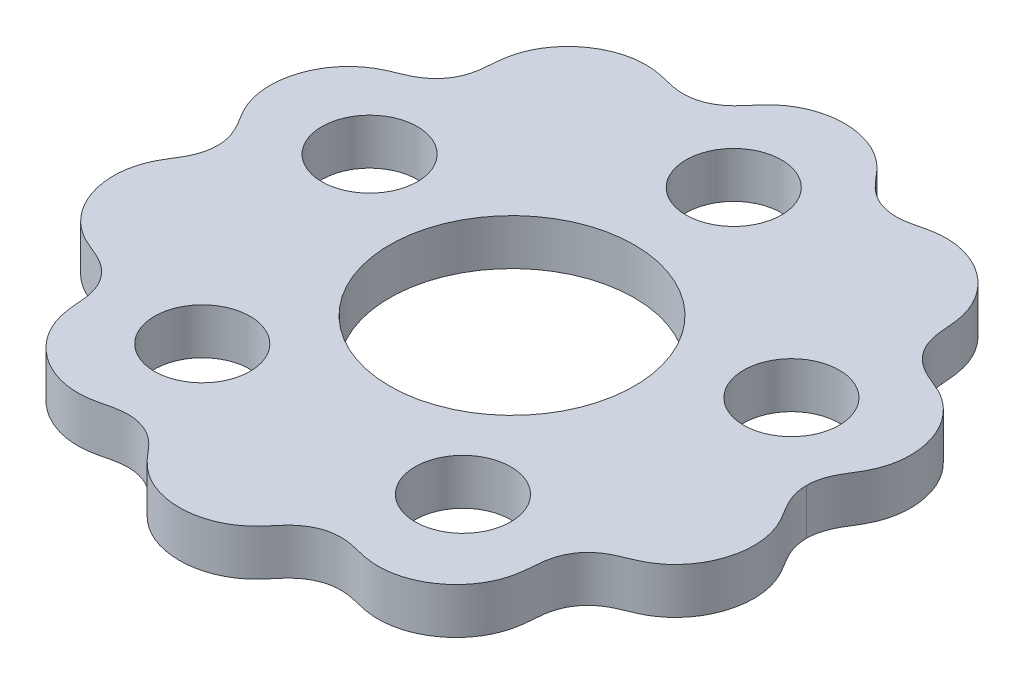
SolidWorks part; units mm, degrees
material "PET"
ref_plane "Front Plane" through (0, 0, 0) normal (0, 0, 1) x (1, 0, 0)
ref_plane "Top Plane" through (0, 0, 0) normal (0, 1, 0) x (1, 0, 0)
ref_plane "Right Plane" through (0, 0, 0) normal (1, 0, 0) x (0, 0, -1)
sketch "Sketch1" plane through (0, 0, 0) normal (0, 1, 0) x (1, 0, 0)
  line L0 (-38.5, 0) -> (38.5, 0) construction
  spline S0 degree 4 poles (41.7399, 11.9357) (41.7976, 11.5909) (41.8823, 10.8959) (41.9166, 9.7895) (41.7622, 8.4507) (41.4548, 7.254) (41.0605, 6.2518) (40.6722, 5.4784) (40.2556, 4.7734) (39.8948, 4.2014) (39.5954, 3.7049) (39.3601, 3.2778) (39.1827, 2.9244) (39.0201, 2.559) (38.8752, 2.1815) (38.7672, 1.8445) (38.689, 1.5515) (38.6338, 1.305) (38.5956, 1.1064) (38.5637, 0.9069) (38.5413, 0.7307) (38.526, 0.5807) (38.516, 0.4563) (38.5095, 0.3545) (38.5047, 0.2479) (38.5015, 0.1386) (38.4995, 0.0148) (38.5001, -0.0789) (38.5036, -0.2237) (38.5098, -0.3594) (38.5164, -0.4628) (38.5267, -0.5886) (38.5424, -0.7399) (38.5653, -0.918) (38.5978, -1.1189) (38.6366, -1.3186) (38.6815, -1.5171) (38.7324, -1.714) (38.8035, -1.9582) (38.914, -2.2894) (39.0778, -2.7023) (39.3093, -3.1893) (39.5914, -3.6994) (39.9929, -4.3618) (40.5108, -5.1772) (41.094, -6.2603) (41.6193, -7.7231) (41.9033, -9.3234) (41.9104, -11.0174) (41.6357, -12.7107) (41.1099, -14.3049) (40.2814, -15.8994) (39.2956, -17.1747) (38.2761, -18.1324) (37.3157, -18.8177) (36.5643, -19.2568) (35.7841, -19.6295) (34.9889, -19.9536) (34.1836, -20.2802) (33.3903, -20.6628) (32.4577, -21.2405) (31.5077, -22.0772) (30.6676, -23.2287) (30.0983, -24.6485) (29.8484, -26.052) (29.7811, -27.3474) (29.672, -28.5202) (29.4293, -29.7204) (28.992, -31.0294) (28.1243, -32.7018) (26.8403, -34.2468) (25.2758, -35.4915) (23.478, -36.4327) (21.9132, -36.9493) (20.3645, -37.183) (18.8855, -37.1588) (17.6433, -36.9754) (16.4953, -36.6867) (15.2652, -36.3845) (13.9169, -36.2413) (12.4319, -36.3844) (11.0762, -36.8709) (9.9712, -37.5729) (9.1322, -38.3356) (8.5282, -39.0054) (7.9812, -39.6642) (7.4483, -40.2769) (6.716, -41.018) (5.6675, -41.866) (4.292, -42.6513) (2.5792, -43.2464) (0.7931, -43.5294) (-0.9374, -43.5172) (-2.6957, -43.2137) (-4.3731, -42.6106) (-5.7196, -41.8284) (-6.7475, -40.9896) (-7.477, -40.2457) (-8.0111, -39.6284) (-8.5572, -38.9713) (-9.1586, -38.3097) (-9.9918, -37.5589) (-11.087, -36.8668) (-12.4351, -36.3841) (-13.9169, -36.2413) (-15.2652, -36.3845) (-16.4953, -36.6867) (-17.6432, -36.9755) (-18.8855, -37.1588) (-20.1014, -37.1787) (-21.2828, -37.0443) (-22.5182, -36.7497) (-23.7112, -36.3106) (-25.2757, -35.4916) (-26.8404, -34.2467) (-28.1243, -32.7018) (-28.992, -31.0294) (-29.4293, -29.7204) (-29.672, -28.5202) (-29.7811, -27.3474) (-29.8484, -26.052) (-30.0983, -24.6485) (-30.6676, -23.2287) (-31.5077, -22.0772) (-32.4577, -21.2405) (-33.3903, -20.6628) (-34.1836, -20.2802) (-34.9889, -19.9536) (-35.7841, -19.6295) (-36.5643, -19.2568) (-37.3157, -18.8177) (-38.2761, -18.1324) (-39.2956, -17.1747) (-40.2814, -15.8994) (-41.2689, -13.9989) (-41.8434, -11.9655) (-41.9616, -10.0978) (-41.7583, -8.4939) (-41.4838, -7.3945) (-41.1825, -6.5281) (-40.8054, -5.7182) (-40.373, -4.9656) (-39.9705, -4.3209) (-39.6284, -3.7649) (-39.3439, -3.2554) (-39.12, -2.7926) (-38.9499, -2.3821) (-38.824, -2.0287) (-38.7172, -1.6695) (-38.6304, -1.304) (-38.5728, -0.9818) (-38.5369, -0.7009) (-38.5162, -0.4703) (-38.5051, -0.2842) (-38.4994, -0.0606) (-38.4996, 0.072) (-38.5059, 0.3106) (-38.5188, 0.5048) (-38.5357, 0.6806) (-38.5541, 0.8315) (-38.5757, 0.9817) (-38.6004, 1.1312) (-38.6338, 1.3049) (-38.689, 1.5516) (-38.7672, 1.8445) (-38.8752, 2.1815) (-39.0201, 2.559) (-39.1827, 2.9244) (-39.3601, 3.2778) (-39.5954, 3.7049) (-39.8948, 4.2014) (-40.2556, 4.7734) (-40.6722, 5.4784) (-41.0605, 6.2518) (-41.4548, 7.254) (-41.7622, 8.4507) (-41.9166, 9.7895) (-41.8823, 10.8959) (-41.7976, 11.5909) (-41.7399, 11.9357) knots 0 0 0 0 0 0.008359 0.016718 0.026378 0.03209 0.037801 0.04242 0.047039 0.051658 0.053968 0.056277 0.058692 0.061108 0.063523 0.065938 0.067146 0.068354 0.069562 0.07077 0.071978 0.072582 0.073186 0.07379 0.074394 0.074998 0.075602 0.076827 0.077439 0.078051 0.078663 0.079275 0.080499 0.081715 0.08293 0.084146 0.085361 0.086577 0.087792 0.090223 0.093706 0.097188 0.10067 0.104152 0.112217 0.120283 0.129997 0.141148 0.150862 0.160575 0.170839 0.181103 0.193621 0.198878 0.204135 0.209266 0.214397 0.219527 0.224658 0.230039 0.23542 0.245691 0.254714 0.26373 0.271663 0.279595 0.285726 0.291856 0.300873 0.312488 0.330522 0.339406 0.34829 0.360829 0.369712 0.376626 0.383539 0.39077 0.398002 0.40689 0.415781 0.426124 0.432044 0.437965 0.442816 0.447666 0.452516 0.457367 0.4677 0.4798 0.490134 0.500468 0.510727 0.520985 0.53259 0.542848 0.547724 0.5526 0.557476 0.562352 0.568152 0.573952 0.584219 0.59311 0.601998 0.60923 0.616461 0.623374 0.630288 0.639171 0.645441 0.65171 0.660594 0.669478 0.687512 0.699127 0.708144 0.714274 0.720405 0.728337 0.73627 0.745286 0.754309 0.76458 0.769961 0.775342 0.780473 0.785603 0.790734 0.795865 0.801122 0.806379 0.818897 0.829161 0.839425 0.857344 0.868978 0.873457 0.877937 0.884404 0.89087 0.894771 0.898672 0.902573 0.906473 0.908713 0.910953 0.913192 0.915432 0.917673 0.919915 0.921035 0.922156 0.923277 0.924398 0.925606 0.926814 0.928022 0.92923 0.929834 0.930438 0.931646 0.932854 0.934062 0.936477 0.938892 0.941308 0.943723 0.946032 0.948342 0.952961 0.95758 0.962199 0.96791 0.973622 0.983282 0.991641 1 1 1 1 1 construction
  spline S1 degree 4 poles (38.5, 0) (38.5, -0.0435) (38.5008, -0.1075) (38.5036, -0.2237) (38.5098, -0.3594) (38.5164, -0.4628) (38.5267, -0.5886) (38.5424, -0.7399) (38.5653, -0.918) (38.5978, -1.1189) (38.6366, -1.3186) (38.6815, -1.5171) (38.7324, -1.714) (38.8035, -1.9582) (38.914, -2.2894) (39.0778, -2.7023) (39.3093, -3.1893) (39.5914, -3.6994) (39.9929, -4.3618) (40.5108, -5.1772) (41.094, -6.2603) (41.6193, -7.7231) (41.9033, -9.3234) (41.9104, -11.0174) (41.6357, -12.7107) (41.1099, -14.3049) (40.2814, -15.8994) (39.2956, -17.1747) (38.2761, -18.1324) (37.3157, -18.8177) (36.5643, -19.2568) (35.7841, -19.6295) (34.9889, -19.9536) (34.1836, -20.2802) (33.3903, -20.6628) (32.4577, -21.2405) (31.5077, -22.0772) (30.6676, -23.2287) (30.0983, -24.6485) (29.8484, -26.052) (29.7811, -27.3474) (29.672, -28.5202) (29.4293, -29.7204) (28.992, -31.0294) (28.1243, -32.7018) (26.8403, -34.2468) (25.2758, -35.4915) (23.478, -36.4327) (21.9132, -36.9493) (20.3645, -37.183) (18.8855, -37.1588) (17.6433, -36.9754) (16.4953, -36.6867) (15.2652, -36.3845) (13.9169, -36.2413) (12.4319, -36.3844) (11.0762, -36.8709) (9.9712, -37.5729) (9.1322, -38.3356) (8.5282, -39.0054) (7.9812, -39.6642) (7.4483, -40.2769) (6.716, -41.018) (5.6675, -41.866) (4.292, -42.6513) (2.5792, -43.2464) (0.7931, -43.5294) (-0.9374, -43.5172) (-2.6957, -43.2137) (-4.3731, -42.6106) (-5.7196, -41.8284) (-6.7475, -40.9896) (-7.477, -40.2457) (-8.0111, -39.6284) (-8.5572, -38.9713) (-9.1586, -38.3097) (-9.9918, -37.5589) (-11.087, -36.8668) (-12.4351, -36.3841) (-13.9169, -36.2413) (-15.2652, -36.3845) (-16.4953, -36.6867) (-17.6432, -36.9755) (-18.8855, -37.1588) (-20.1014, -37.1787) (-21.2828, -37.0443) (-22.5182, -36.7497) (-23.7112, -36.3106) (-25.2757, -35.4916) (-26.8404, -34.2467) (-28.1243, -32.7018) (-28.992, -31.0294) (-29.4293, -29.7204) (-29.672, -28.5202) (-29.7811, -27.3474) (-29.8484, -26.052) (-30.0983, -24.6485) (-30.6676, -23.2287) (-31.5077, -22.0772) (-32.4577, -21.2405) (-33.3903, -20.6628) (-34.1836, -20.2802) (-34.9889, -19.9536) (-35.7841, -19.6295) (-36.5643, -19.2568) (-37.3157, -18.8177) (-38.2761, -18.1324) (-39.2956, -17.1747) (-40.2814, -15.8994) (-41.2689, -13.9989) (-41.8434, -11.9655) (-41.9616, -10.0978) (-41.7583, -8.4939) (-41.4838, -7.3945) (-41.1825, -6.5281) (-40.8054, -5.7182) (-40.373, -4.9656) (-39.9705, -4.3209) (-39.6284, -3.7649) (-39.3439, -3.2554) (-39.12, -2.7926) (-38.9499, -2.3821) (-38.824, -2.0287) (-38.7172, -1.6695) (-38.6304, -1.304) (-38.5728, -0.9818) (-38.5369, -0.7009) (-38.5162, -0.4703) (-38.5051, -0.2842) (-38.5009, -0.1197) (-38.5, -0.0398) (-38.5, 0) knots 0.075602 0.075602 0.075602 0.075602 0.075602 0.076827 0.077439 0.078051 0.078663 0.079275 0.080499 0.081715 0.08293 0.084146 0.085361 0.086577 0.087792 0.090223 0.093706 0.097188 0.10067 0.104152 0.112217 0.120283 0.129997 0.141148 0.150862 0.160575 0.170839 0.181103 0.193621 0.198878 0.204135 0.209266 0.214397 0.219527 0.224658 0.230039 0.23542 0.245691 0.254714 0.26373 0.271663 0.279595 0.285726 0.291856 0.300873 0.312488 0.330522 0.339406 0.34829 0.360829 0.369712 0.376626 0.383539 0.39077 0.398002 0.40689 0.415781 0.426124 0.432044 0.437965 0.442816 0.447666 0.452516 0.457367 0.4677 0.4798 0.490134 0.500468 0.510727 0.520985 0.53259 0.542848 0.547724 0.5526 0.557476 0.562352 0.568152 0.573952 0.584219 0.59311 0.601998 0.60923 0.616461 0.623374 0.630288 0.639171 0.645441 0.65171 0.660594 0.669478 0.687512 0.699127 0.708144 0.714274 0.720405 0.728337 0.73627 0.745286 0.754309 0.76458 0.769961 0.775342 0.780473 0.785603 0.790734 0.795865 0.801122 0.806379 0.818897 0.829161 0.839425 0.857344 0.868978 0.873457 0.877937 0.884404 0.89087 0.894771 0.898672 0.902573 0.906473 0.908713 0.910953 0.913192 0.915432 0.917673 0.919915 0.921035 0.922156 0.923277 0.924398 0.924398 0.924398 0.924398 0.924398
  spline S3 degree 4 poles (38.5, 0) (38.5, 0.0435) (38.5008, 0.1075) (38.5036, 0.2237) (38.5098, 0.3594) (38.5164, 0.4628) (38.5267, 0.5886) (38.5424, 0.7399) (38.5653, 0.918) (38.5978, 1.1189) (38.6366, 1.3186) (38.6815, 1.5171) (38.7324, 1.714) (38.8035, 1.9582) (38.914, 2.2894) (39.0778, 2.7023) (39.3093, 3.1893) (39.5914, 3.6994) (39.9929, 4.3618) (40.5108, 5.1772) (41.094, 6.2603) (41.6193, 7.7231) (41.9033, 9.3234) (41.9104, 11.0174) (41.6357, 12.7107) (41.1099, 14.3049) (40.2814, 15.8994) (39.2956, 17.1747) (38.2761, 18.1324) (37.3157, 18.8177) (36.5643, 19.2568) (35.7841, 19.6295) (34.9889, 19.9536) (34.1836, 20.2802) (33.3903, 20.6628) (32.4577, 21.2405) (31.5077, 22.0772) (30.6676, 23.2287) (30.0983, 24.6485) (29.8484, 26.052) (29.7811, 27.3474) (29.672, 28.5202) (29.4293, 29.7204) (28.992, 31.0294) (28.1243, 32.7018) (26.8403, 34.2468) (25.2758, 35.4915) (23.478, 36.4327) (21.9132, 36.9493) (20.3645, 37.183) (18.8855, 37.1588) (17.6433, 36.9754) (16.4953, 36.6867) (15.2652, 36.3845) (13.9169, 36.2413) (12.4319, 36.3844) (11.0762, 36.8709) (9.9712, 37.5729) (9.1322, 38.3356) (8.5282, 39.0054) (7.9812, 39.6642) (7.4483, 40.2769) (6.716, 41.018) (5.6675, 41.866) (4.292, 42.6513) (2.5792, 43.2464) (0.7931, 43.5294) (-0.9374, 43.5172) (-2.6957, 43.2137) (-4.3731, 42.6106) (-5.7196, 41.8284) (-6.7475, 40.9896) (-7.477, 40.2457) (-8.0111, 39.6284) (-8.5572, 38.9713) (-9.1586, 38.3097) (-9.9918, 37.5589) (-11.087, 36.8668) (-12.4351, 36.3841) (-13.9169, 36.2413) (-15.2652, 36.3845) (-16.4953, 36.6867) (-17.6432, 36.9755) (-18.8855, 37.1588) (-20.1014, 37.1787) (-21.2828, 37.0443) (-22.5182, 36.7497) (-23.7112, 36.3106) (-25.2757, 35.4916) (-26.8404, 34.2467) (-28.1243, 32.7018) (-28.992, 31.0294) (-29.4293, 29.7204) (-29.672, 28.5202) (-29.7811, 27.3474) (-29.8484, 26.052) (-30.0983, 24.6485) (-30.6676, 23.2287) (-31.5077, 22.0772) (-32.4577, 21.2405) (-33.3903, 20.6628) (-34.1836, 20.2802) (-34.9889, 19.9536) (-35.7841, 19.6295) (-36.5643, 19.2568) (-37.3157, 18.8177) (-38.2761, 18.1324) (-39.2956, 17.1747) (-40.2814, 15.8994) (-41.2689, 13.9989) (-41.8434, 11.9655) (-41.9616, 10.0978) (-41.7583, 8.4939) (-41.4838, 7.3945) (-41.1825, 6.5281) (-40.8054, 5.7182) (-40.373, 4.9656) (-39.9705, 4.3209) (-39.6284, 3.7649) (-39.3439, 3.2554) (-39.12, 2.7926) (-38.9499, 2.3821) (-38.824, 2.0287) (-38.7172, 1.6695) (-38.6304, 1.304) (-38.5728, 0.9818) (-38.5369, 0.7009) (-38.5162, 0.4703) (-38.5051, 0.2842) (-38.5009, 0.1197) (-38.5, 0.0398) (-38.5, 0) knots 0.075602 0.075602 0.075602 0.075602 0.075602 0.076827 0.077439 0.078051 0.078663 0.079275 0.080499 0.081715 0.08293 0.084146 0.085361 0.086577 0.087792 0.090223 0.093706 0.097188 0.10067 0.104152 0.112217 0.120283 0.129997 0.141148 0.150862 0.160575 0.170839 0.181103 0.193621 0.198878 0.204135 0.209266 0.214397 0.219527 0.224658 0.230039 0.23542 0.245691 0.254714 0.26373 0.271663 0.279595 0.285726 0.291856 0.300873 0.312488 0.330522 0.339406 0.34829 0.360829 0.369712 0.376626 0.383539 0.39077 0.398002 0.40689 0.415781 0.426124 0.432044 0.437965 0.442816 0.447666 0.452516 0.457367 0.4677 0.4798 0.490134 0.500468 0.510727 0.520985 0.53259 0.542848 0.547724 0.5526 0.557476 0.562352 0.568152 0.573952 0.584219 0.59311 0.601998 0.60923 0.616461 0.623374 0.630288 0.639171 0.645441 0.65171 0.660594 0.669478 0.687512 0.699127 0.708144 0.714274 0.720405 0.728337 0.73627 0.745286 0.754309 0.76458 0.769961 0.775342 0.780473 0.785603 0.790734 0.795865 0.801122 0.806379 0.818897 0.829161 0.839425 0.857344 0.868978 0.873457 0.877937 0.884404 0.89087 0.894771 0.898672 0.902573 0.906473 0.908713 0.910953 0.913192 0.915432 0.917673 0.919915 0.921035 0.922156 0.923277 0.924398 0.924398 0.924398 0.924398 0.924398
extrude "Boss-Extrude1" add sketch "Sketch1" along normal blind 6
sketch "Sketch2" plane through (0, 6, 0) normal (0, 1, 0) x (1, 0, 0)
  line L0 (0, 0) -> (38.5, 0) construction
  line L1 (0, 0) -> (41.371, 13.4423) construction
  circle A0 centre (0, 0) radius 16
  circle A1 centre (27.5801, 8.9631) radius 6.25
  circle A2 centre (17.0471, -23.4605) radius 6.25
  circle A3 centre (-17.0444, -23.4625) radius 6.25
  circle A4 centre (-27.5812, 8.9599) radius 6.25
  circle A5 centre (-0.0017, 29) radius 6.25
  spline S1 degree 4 poles (38.5, 0) (38.5, 0.0435) (38.5008, 0.1075) (38.5036, 0.2237) (38.5098, 0.3594) (38.5164, 0.4628) (38.5267, 0.5886) (38.5424, 0.7399) (38.5653, 0.918) (38.5978, 1.1189) (38.6366, 1.3186) (38.6815, 1.5171) (38.7324, 1.714) (38.8035, 1.9582) (38.914, 2.2894) (39.0778, 2.7023) (39.3093, 3.1893) (39.5914, 3.6994) (39.9929, 4.3618) (40.5108, 5.1772) (41.094, 6.2603) (41.6193, 7.7231) (41.9033, 9.3234) (41.9104, 11.0174) (41.6357, 12.7107) (41.1099, 14.3049) (40.2814, 15.8994) (39.2956, 17.1747) (38.2761, 18.1324) (37.3157, 18.8177) (36.5643, 19.2568) (35.7841, 19.6295) (34.9889, 19.9536) (34.1836, 20.2802) (33.3903, 20.6628) (32.4577, 21.2405) (31.5077, 22.0772) (30.6676, 23.2287) (30.0983, 24.6485) (29.8484, 26.052) (29.7811, 27.3474) (29.672, 28.5202) (29.4293, 29.7204) (28.992, 31.0294) (28.1243, 32.7018) (26.8403, 34.2468) (25.2758, 35.4915) (23.478, 36.4327) (21.9132, 36.9493) (20.3645, 37.183) (18.8855, 37.1588) (17.6433, 36.9754) (16.4953, 36.6867) (15.2652, 36.3845) (13.9169, 36.2413) (12.4319, 36.3844) (11.0762, 36.8709) (9.9712, 37.5729) (9.1322, 38.3356) (8.5282, 39.0054) (7.9812, 39.6642) (7.4483, 40.2769) (6.716, 41.018) (5.6675, 41.866) (4.292, 42.6513) (2.5792, 43.2464) (0.7931, 43.5294) (-0.9374, 43.5172) (-2.6957, 43.2137) (-4.3731, 42.6106) (-5.7196, 41.8284) (-6.7475, 40.9896) (-7.477, 40.2457) (-8.0111, 39.6284) (-8.5572, 38.9713) (-9.1586, 38.3097) (-9.9918, 37.5589) (-11.087, 36.8668) (-12.4351, 36.3841) (-13.9169, 36.2413) (-15.2652, 36.3845) (-16.4953, 36.6867) (-17.6432, 36.9755) (-18.8855, 37.1588) (-20.1014, 37.1787) (-21.2828, 37.0443) (-22.5182, 36.7497) (-23.7112, 36.3106) (-25.2757, 35.4916) (-26.8404, 34.2467) (-28.1243, 32.7018) (-28.992, 31.0294) (-29.4293, 29.7204) (-29.672, 28.5202) (-29.7811, 27.3474) (-29.8484, 26.052) (-30.0983, 24.6485) (-30.6676, 23.2287) (-31.5077, 22.0772) (-32.4577, 21.2405) (-33.3903, 20.6628) (-34.1836, 20.2802) (-34.9889, 19.9536) (-35.7841, 19.6295) (-36.5643, 19.2568) (-37.3157, 18.8177) (-38.2761, 18.1324) (-39.2956, 17.1747) (-40.2814, 15.8994) (-41.2689, 13.9989) (-41.8434, 11.9655) (-41.9616, 10.0978) (-41.7583, 8.4939) (-41.4838, 7.3945) (-41.1825, 6.5281) (-40.8054, 5.7182) (-40.373, 4.9656) (-39.9705, 4.3209) (-39.6284, 3.7649) (-39.3439, 3.2554) (-39.12, 2.7926) (-38.9499, 2.3821) (-38.824, 2.0287) (-38.7172, 1.6695) (-38.6304, 1.304) (-38.5728, 0.9818) (-38.5369, 0.7009) (-38.5162, 0.4703) (-38.5051, 0.2842) (-38.5009, 0.1197) (-38.5, 0.0398) (-38.5, 0) knots 0.075602 0.075602 0.075602 0.075602 0.075602 0.076827 0.077439 0.078051 0.078663 0.079275 0.080499 0.081715 0.08293 0.084146 0.085361 0.086577 0.087792 0.090223 0.093706 0.097188 0.10067 0.104152 0.112217 0.120283 0.129997 0.141148 0.150862 0.160575 0.170839 0.181103 0.193621 0.198878 0.204135 0.209266 0.214397 0.219527 0.224658 0.230039 0.23542 0.245691 0.254714 0.26373 0.271663 0.279595 0.285726 0.291856 0.300873 0.312488 0.330522 0.339406 0.34829 0.360829 0.369712 0.376626 0.383539 0.39077 0.398002 0.40689 0.415781 0.426124 0.432044 0.437965 0.442816 0.447666 0.452516 0.457367 0.4677 0.4798 0.490134 0.500468 0.510727 0.520985 0.53259 0.542848 0.547724 0.5526 0.557476 0.562352 0.568152 0.573952 0.584219 0.59311 0.601998 0.60923 0.616461 0.623374 0.630288 0.639171 0.645441 0.65171 0.660594 0.669478 0.687512 0.699127 0.708144 0.714274 0.720405 0.728337 0.73627 0.745286 0.754309 0.76458 0.769961 0.775342 0.780473 0.785603 0.790734 0.795865 0.801122 0.806379 0.818897 0.829161 0.839425 0.857344 0.868978 0.873457 0.877937 0.884404 0.89087 0.894771 0.898672 0.902573 0.906473 0.908713 0.910953 0.913192 0.915432 0.917673 0.919915 0.921035 0.922156 0.923277 0.924398 0.924398 0.924398 0.924398 0.924398 construction
  point P21 (0, 0)
  dimension "D1" = 32
  dimension "D2" = 12.5
  dimension "D3" = 29
  dimension "D4" = 5
extrude "Cut-Extrude1" cut sketch "Sketch2" against normal blind 19
